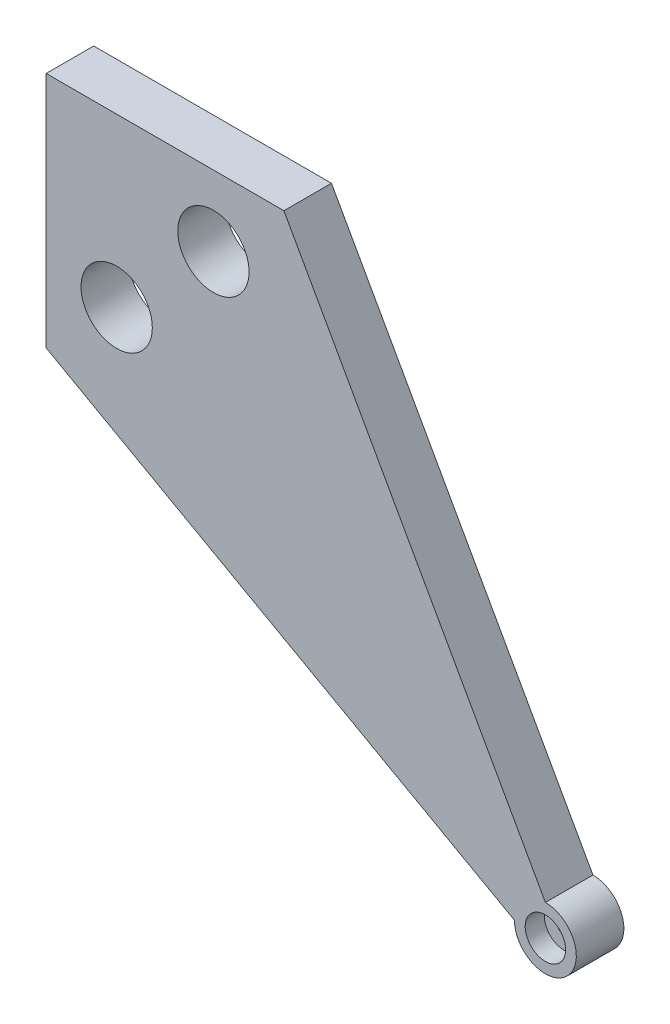
SolidWorks part; units mm, degrees
ref_plane "Plano frontal" through (0, 0, 0) normal (0, 0, 1) x (1, 0, 0)
ref_plane "Plano superior" through (0, 0, 0) normal (0, 1, 0) x (1, 0, 0)
ref_plane "Plano direito" through (0, 0, 0) normal (1, 0, 0) x (0, 0, -1)
sketch "Esboço3" plane through (0, 0, 0) normal (0, 0, 1) x (1, 0, 0)
  line L0 (-62.966, 0) -> (106.6858, 0) construction
  line L1 (0, 69.7378) -> (0, -73.302) construction
  line L2 (0, 50) -> (98.5, 105)
  line L3 (0, 0) -> (50, 0)
  line L4 (0, 0) -> (0, 50)
  line L7 (50, 0) -> (105, 98.5)
  arc A0 (105, 98.5) -> (98.5, 105) centre (105, 105) ccw
  dimension "D4" = 105
  dimension "D5" = 13
  dimension "D3" = 105
extrude "Ressalto-extrusão2" add sketch "Esboço3" along normal mid plane 10
sketch "Esboço4" plane through (0, 0, 5) normal (0, 0, 1) x (1, 0, 0)
  circle A0 centre (105, 105) radius 4.25
  arc A1 (105, 98.5) -> (98.5, 105) centre (105, 105) ccw construction
  dimension "D1" = 8.5
extrude "Corte-extrusão1" cut sketch "Esboço4" against normal blind 4 contours A0
sketch "Esboço5" plane through (0, 0, 1) normal (0, 0, 1) x (1, 0, 0)
  circle A0 centre (105, 105) radius 1.5
  circle A1 centre (105, 105) radius 4.25 construction
extrude "Corte-extrusão2" cut sketch "Esboço5" against normal through all
sketch "Esboço6" plane through (0, 0, 5) normal (0, 0, 1) x (1, 0, 0)
  line L0 (-26.6702, 0) -> (72.5742, 0) construction
  line L1 (0, 62.2144) -> (0, -11.4301) construction
  line L2 (0, 50) -> (63.2897, 50) construction
  line L3 (50, 0) -> (50, 50) construction
  line L4 (0, 50) -> (14.8256, 35.1744) construction
  line L5 (14.8256, 35.1744) -> (35.1744, 14.8256) construction
  line L6 (35.1744, 14.8256) -> (50, 0) construction
  line L7 (0, 0) -> (50, 50) construction
  circle A0 centre (14.8256, 35.1744) radius 7.5
  circle A1 centre (35.1744, 14.8256) radius 7.5
  point P16 (0, 0)
  dimension "D1" = 15
  dimension "D2" = 15
extrude "Corte-extrusão3" cut sketch "Esboço6" against normal through all
mirror "Espelhar1" about plane through (0, 0, 5) normal (0, 1, 0) of bodies 105
mirror "Espelhar2" about plane through (0, 0, 5) normal (1, 0, 0) of bodies 106 105
delete or keep bodies "Corpo-Excluir/Manter 1" type delete bodies bodies 108
delete or keep bodies "Corpo-Excluir/Manter 2" type delete bodies bodies 105
delete or keep bodies "Corpo-Excluir/Manter 3" type delete bodies bodies 107
